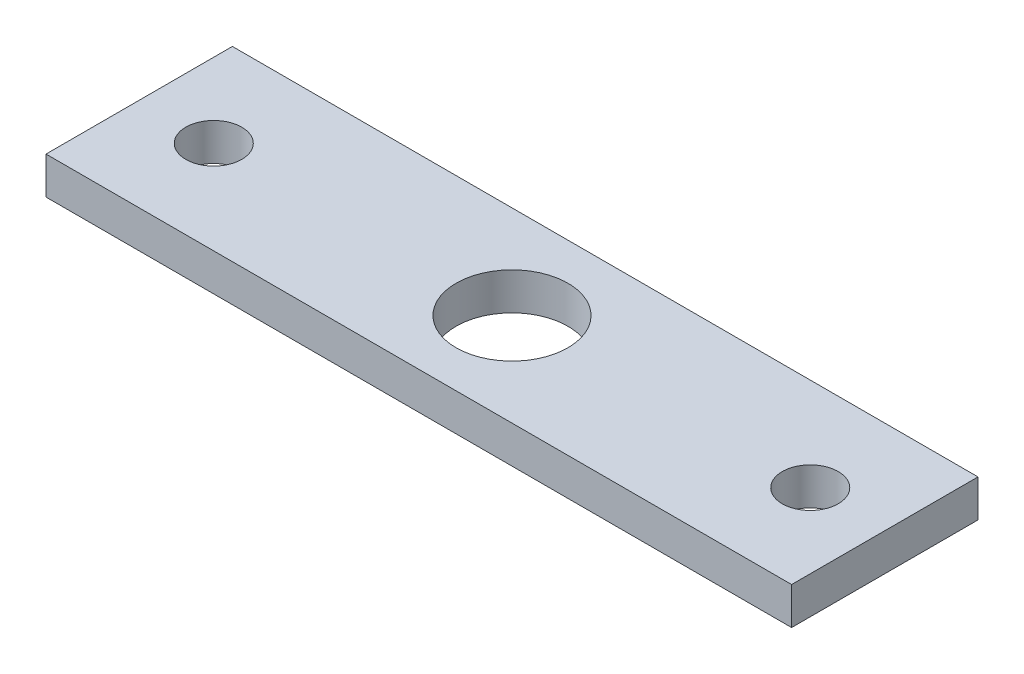
SolidWorks part; units mm, degrees
ref_plane "Front Plane" through (0, 0, 0) normal (0, 0, 1) x (1, 0, 0)
ref_plane "Top Plane" through (0, 0, 0) normal (0, 1, 0) x (1, 0, 0)
ref_plane "Right Plane" through (0, 0, 0) normal (1, 0, 0) x (0, 0, -1)
sketch "Sketch1" plane through (0, 0, 0) normal (0, 1, 0) x (1, 0, 0)
  line L1 (-33.3333, 5.1316) -> (6.6667, 5.1316)
  line L2 (-33.3333, 5.1316) -> (-33.3333, -4.8684)
  line L3 (-33.3333, -4.8684) -> (6.6667, -4.8684)
  line L4 (6.6667, 5.1316) -> (6.6667, -4.8684)
  dimension "D1" = 10
  dimension "D2" = 40
extrude "Boss-Extrude1" add sketch "Sketch1" along normal blind 2
sketch "Sketch2" plane through (0, 2, 0) normal (0, 1, 0) x (1, 0, 0)
  line L0 (-33.3333, 5.1316) -> (-33.3333, -4.8684) construction
  line L1 (-33.3333, -4.8684) -> (6.6667, -4.8684) construction
  line L3 (6.6667, 5.1316) -> (-33.3333, 5.1316) construction
  circle A0 centre (-29.3333, 0.1316) radius 1.5
  circle A1 centre (2.6667, 0.1316) radius 1.5
  circle A2 centre (-13.3333, 0.1316) radius 3
  dimension "D2" = 3
  dimension "D3" = 3
  dimension "D7" = 6
  dimension "D1" = 32
  dimension "D4" = 4
  dimension "D5" = 5
  dimension "D6" = 5
  dimension "D8" = 16
  dimension "D9" = 5
extrude "Cut-Extrude1" cut sketch "Sketch2" against normal through all
